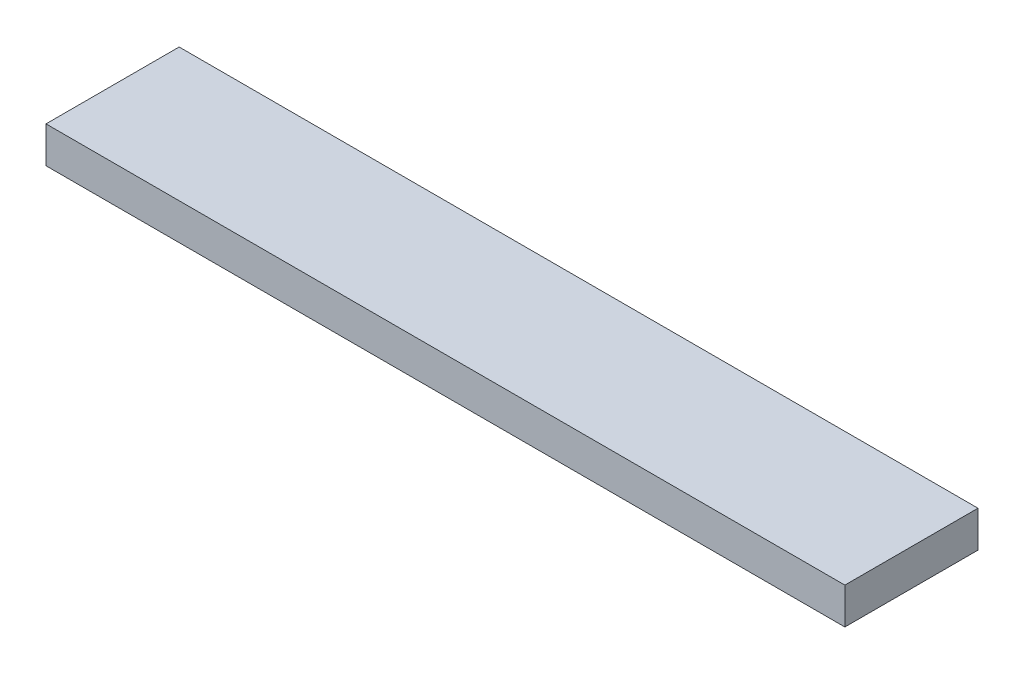
SolidWorks part; units mm, degrees
ref_plane "Front Plane" through (0, 0, 0) normal (0, 0, 1) x (1, 0, 0)
ref_plane "Top Plane" through (0, 0, 0) normal (0, 1, 0) x (1, 0, 0)
ref_plane "Right Plane" through (0, 0, 0) normal (1, 0, 0) x (0, 0, -1)
sketch "Sketch1" plane through (0, 0, 0) normal (0, 1, 0) x (1, 0, 0)
  line L1 (0, 0) -> (838.2, 0)
  line L2 (0, 0) -> (0, 139.7)
  line L3 (0, 139.7) -> (838.2, 139.7)
  line L4 (838.2, 0) -> (838.2, 139.7)
  dimension "D1" = 139.7
  dimension "D2" = 838.2
extrude "Boss-Extrude1" add sketch "Sketch1" along normal blind 38.1
